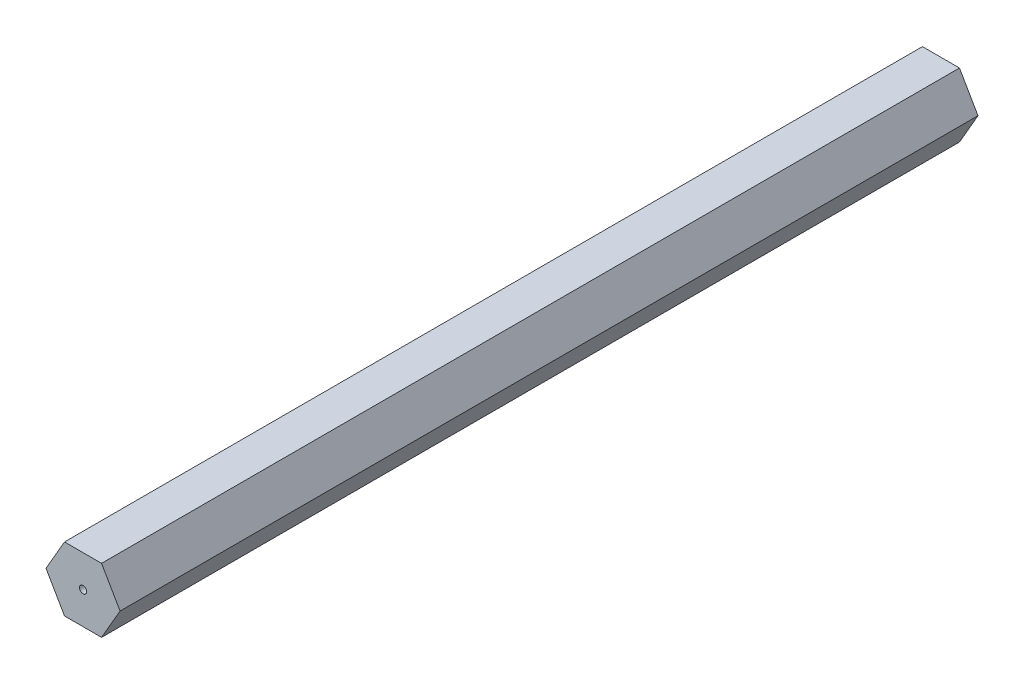
SolidWorks part; units mm, degrees
material "6061-T6 (SS)"
ref_plane "Front Plane" through (0, 0, 0) normal (0, 0, 1) x (1, 0, 0)
ref_plane "Top Plane" through (0, 0, 0) normal (0, 1, 0) x (1, 0, 0)
ref_plane "Right Plane" through (0, 0, 0) normal (1, 0, 0) x (0, 0, -1)
sketch "Sketch1" plane through (0, 0, 0) normal (0, 0, 1) x (1, 0, 0)
  line L1 (3.6662, -6.35) -> (7.3323, 0)
  line L2 (7.3323, 0) -> (3.6662, 6.35)
  line L3 (3.6662, 6.35) -> (-3.6662, 6.35)
  line L4 (-3.6662, 6.35) -> (-7.3323, 0)
  line L5 (-7.3323, 0) -> (-3.6662, -6.35)
  line L6 (-3.6662, -6.35) -> (3.6662, -6.35)
  circle A0 centre (0, 0) radius 6.35 construction
  dimension "D1" = 12.7
extrude "Boss-Extrude1" add sketch "Sketch1" along normal blind 169.8625
sketch "Sketch2" plane through (0, 0, 169.8625) normal (0, 0, 1) x (1, 0, 0)
  circle A0 centre (0, 0) radius 0.71
extrude "Cut-Extrude1" cut sketch "Sketch2" against normal through all
